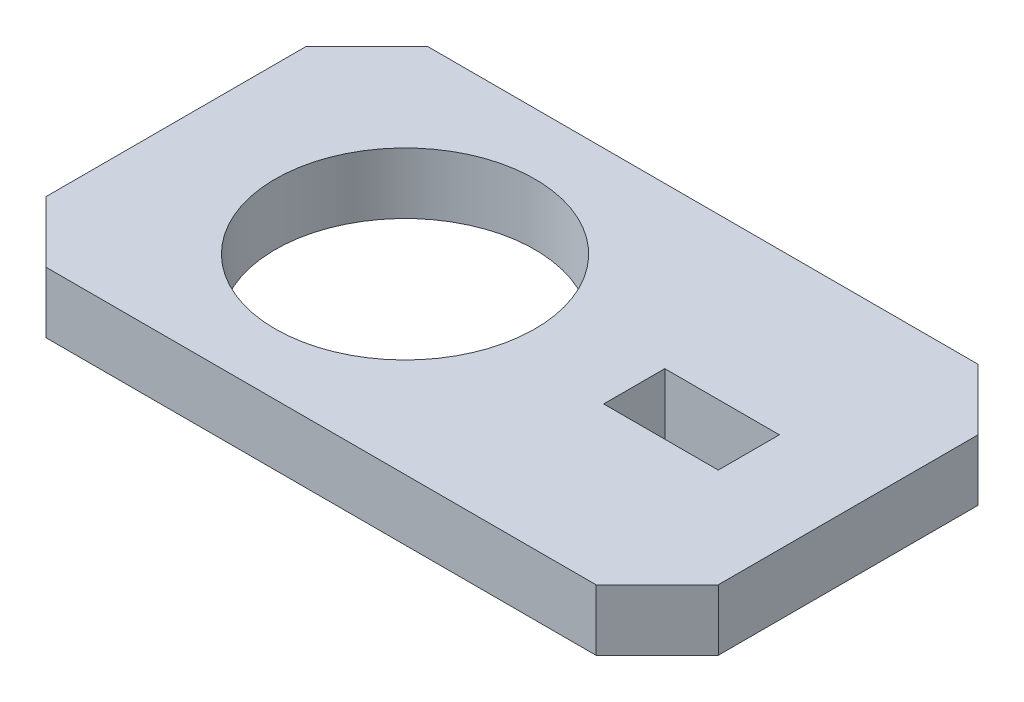
SolidWorks part; units mm, degrees
material "Pine"
ref_plane "Front Plane" through (0, 0, 0) normal (0, 0, 1) x (1, 0, 0)
ref_plane "Top Plane" through (0, 0, 0) normal (0, 1, 0) x (1, 0, 0)
ref_plane "Right Plane" through (0, 0, 0) normal (1, 0, 0) x (0, 0, -1)
sketch "Sketch1" plane through (0, 0, 0) normal (0, 1, 0) x (1, 0, 0)
  line L1 (0, 0) -> (44, 0)
  line L2 (0, 0) -> (0, 25)
  line L3 (0, 25) -> (44, 25)
  line L4 (44, 0) -> (44, 25)
  line L5 (30, 10.5) -> (37.5, 10.5)
  line L6 (30, 10.5) -> (30, 14.5)
  line L7 (30, 14.5) -> (37.5, 14.5)
  line L8 (37.5, 10.5) -> (37.5, 14.5)
  circle A0 centre (15, 12.5) radius 8.5
  point P7 (0, 12.5)
  point P12 (30, 12.5)
  dimension "D3" = 17
  dimension "D1" = 44
  dimension "D2" = 25
  dimension "D4" = 7.5
  dimension "D5" = 4
  dimension "D6" = 29
  dimension "D7" = 14
extrude "Boss-Extrude1" add sketch "Sketch1" along normal blind 4
chamfer "Chamfer1" distance 4 angle 45 4 edges at (0, 2, 0) (0, 2, -25) (44, 2, -25) (44, 2, 0)
